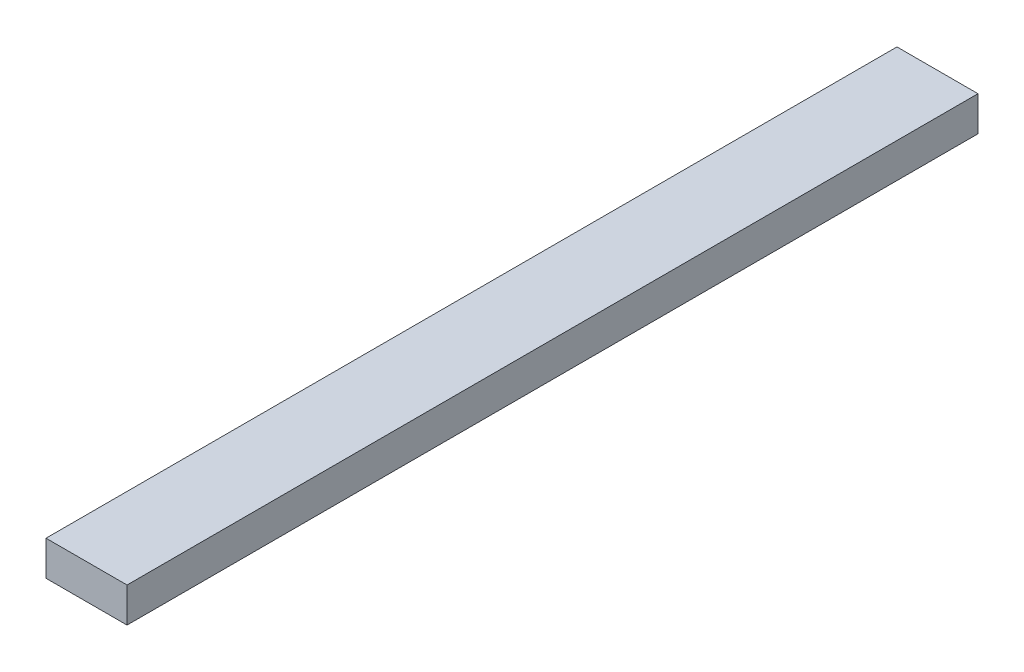
SolidWorks part; units mm, degrees
material "Pine"
ref_plane "Front Plane" through (0, 0, 0) normal (0, 0, 1) x (1, 0, 0)
ref_plane "Top Plane" through (0, 0, 0) normal (0, 1, 0) x (1, 0, 0)
ref_plane "Right Plane" through (0, 0, 0) normal (1, 0, 0) x (0, 0, -1)
sketch "Sketch1" plane through (0, 0, 0) normal (0, 0, 1) x (1, 0, 0)
  line L1 (-58.8508, 47.0281) -> (30.0492, 47.0281)
  line L2 (-58.8508, 47.0281) -> (-58.8508, 8.9281)
  line L3 (-58.8508, 8.9281) -> (30.0492, 8.9281)
  line L4 (30.0492, 47.0281) -> (30.0492, 8.9281)
  dimension "D1" = 38.1
  dimension "D2" = 88.9
extrude "Boss-Extrude1" add sketch "Sketch1" along normal blind 933.45
equation "\"3600n\"=36.75"
